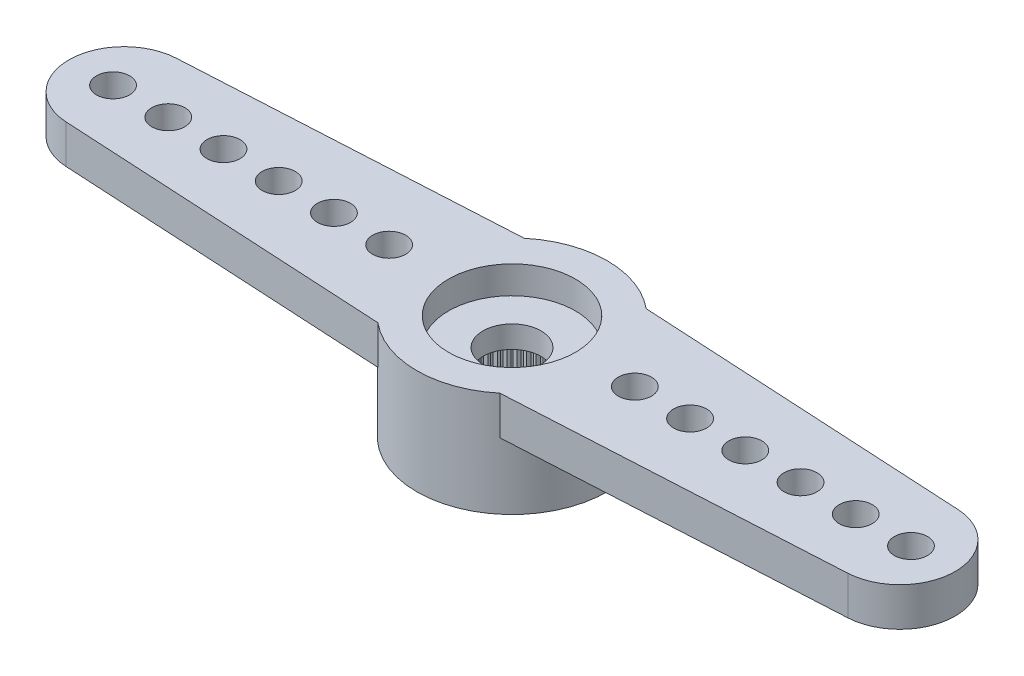
SolidWorks part; units mm, degrees
material "普通碳钢"
ref_plane "Plano frontal" through (0, 0, 0) normal (0, 0, 1) x (1, 0, 0)
ref_plane "Plano superior" through (0, 0, 0) normal (0, 1, 0) x (1, 0, 0)
ref_plane "Plano direito" through (0, 0, 0) normal (1, 0, 0) x (0, 0, -1)
sketch "Esboço1" plane through (0, 0, 0) normal (0, 1, 0) x (1, 0, 0)
  line L0 (0, 0) -> (-14.05, 0) construction
  line L1 (-14.1591, 1.997) -> (-2.2091, 2.65)
  line L2 (-2.2091, -2.65) -> (-14.1591, -1.997)
  arc A0 (-2.2091, -2.65) -> (-2.2091, 2.65) centre (0, 0) ccw
  arc A1 (-14.1591, 1.997) -> (-14.1591, -1.997) centre (-14.05, 0) ccw
  dimension "D1" = 6.9
  dimension "D2" = 4
  dimension "D3" = 19.5
  dimension "D4" = 5.3
extrude "Ressalto-extrusão1" add sketch "Esboço1" against normal blind 1.4
sketch "Esboço2" plane through (0, -1.4, 0) normal (0, -1, 0) x (1, 0, 0)
  arc A0 (-2.2091, -2.65) -> (-2.2091, 2.65) centre (0, 0) ccw construction
  circle A1 centre (0, 0) radius 3.45
extrude "Ressalto-extrusão2" add sketch "Esboço2" along normal offset from surface (2.4 mm away) 3.8 up to face at (-7.242, 0, 0)
hole_wizard "Furo4" positions "Esboço9" profile "Esboço10" legacy end condition through all
sketch "Esboço9" plane through (0, 0, 0) normal (0, 1, 0) x (1, 0, 0)
  line L1 (-14.45, 0) -> (0, 0) construction
  arc A2 (-14.1591, 1.997) -> (-14.1591, -1.997) centre (-14.05, 0) ccw construction
  point P0 (-14.45, 0)
  point P19 (-16.05, 0)
  dimension "D1" = 1.6
sketch "Esboço10" plane through (-14.45, 0, 0) normal (1, 0, 0) x (0, 0, 1)
  line L0 (0, 0) -> (0, 3.8)
  line L1 (0, 3.8) -> (0.6, 3.8)
  line L2 (0.6, 3.8) -> (0.6, 0)
  line L3 (0.6, 0) -> (0, 0)
  line L4 (0, 110) -> (0, -10) construction
  dimension "Diameter" = 1.2
  dimension "Depth" = 3.8
pattern_linear "Padrão linear1" count 6 spacing 2 along (1, 0, 0) of "Furo4"
pattern_circular "PadrãoCircular2" count 2 over 360 about axis through (0, 0, 0) along (0, 1, 0) of "Ressalto-extrusão1", "Furo4", "Padrão linear1"
hole_wizard "Furo1" positions "Esboço3" profile "Esboço4" legacy
sketch "Esboço3" plane through (0, -3.8, 0) normal (0, -1, 0) x (-1, 0, 0)
  point P0 (0, 0)
sketch "Esboço4" plane through (0, -3.8, 0) normal (1, 0, 0) x (0, 0, -1)
  line L0 (0, 0) -> (0, 2)
  line L1 (0, 2) -> (2.475, 2)
  line L2 (2.475, 2) -> (2.475, 0)
  line L3 (2.475, 0) -> (0, 0)
  line L4 (0, 110) -> (0, -10) construction
  dimension "Diameter" = 4.95
  dimension "Depth" = 2
hole_wizard "Furo2" positions "Esboço5" profile "Esboço6" legacy
sketch "Esboço5" plane through (0, 0, 0) normal (0, 1, 0) x (1, 0, 0)
  point P0 (0, 0)
sketch "Esboço6" plane through (0, 0, 0) normal (1, 0, 0) x (0, 0, 1)
  line L0 (0, 0) -> (0, 1)
  line L1 (0, 1) -> (2.3, 1)
  line L2 (2.3, 1) -> (2.3, 0)
  line L3 (2.3, 0) -> (0, 0)
  line L4 (0, 110) -> (0, -10) construction
  dimension "Diameter" = 4.6
  dimension "Depth" = 1
hole_wizard "Furo3" positions "Esboço7" profile "Esboço8" legacy end condition through all
sketch "Esboço7" plane through (0, 0, 0) normal (0, 1, 0) x (1, 0, 0)
  point P0 (0, 0)
sketch "Esboço8" plane through (0, 0, 0) normal (1, 0, 0) x (0, 0, 1)
  line L0 (0, 0) -> (0, 3.8)
  line L1 (0, 3.8) -> (1.05, 3.8)
  line L2 (1.05, 3.8) -> (1.05, 0)
  line L3 (1.05, 0) -> (0, 0)
  line L4 (0, 110) -> (0, -10) construction
  dimension "Diameter" = 2.1
  dimension "Depth" = 3.8
sketch "Esboço11" plane through (0, -3.8, 0) normal (0, -1, 0) x (1, 0, 0)
  line L0 (-0.0981, 2.4731) -> (0, 2.375)
  line L1 (0, 2.375) -> (0.0981, 2.4731)
  line L2 (0, 0) -> (0, 2.475) construction
  circle A0 centre (0, 0) radius 2.375 construction
  circle A1 centre (0, 0) radius 2.475
  arc A2 (0.0981, 2.4731) -> (-0.0981, 2.4731) centre (0, 0) ccw
  dimension "D3" = 4.75
  dimension "D2" = 0.1
  dimension "D1" = 0
extrude "Ressalto-extrusão3" add sketch "Esboço11" against normal up to surface (2 mm away) up to face at (0, -1.8, 1.05)
pattern_circular "PadrãoCircular1" count 60 over 360 about axis through (0, 0, 0) along (0, 1, 0) of "Ressalto-extrusão3"
